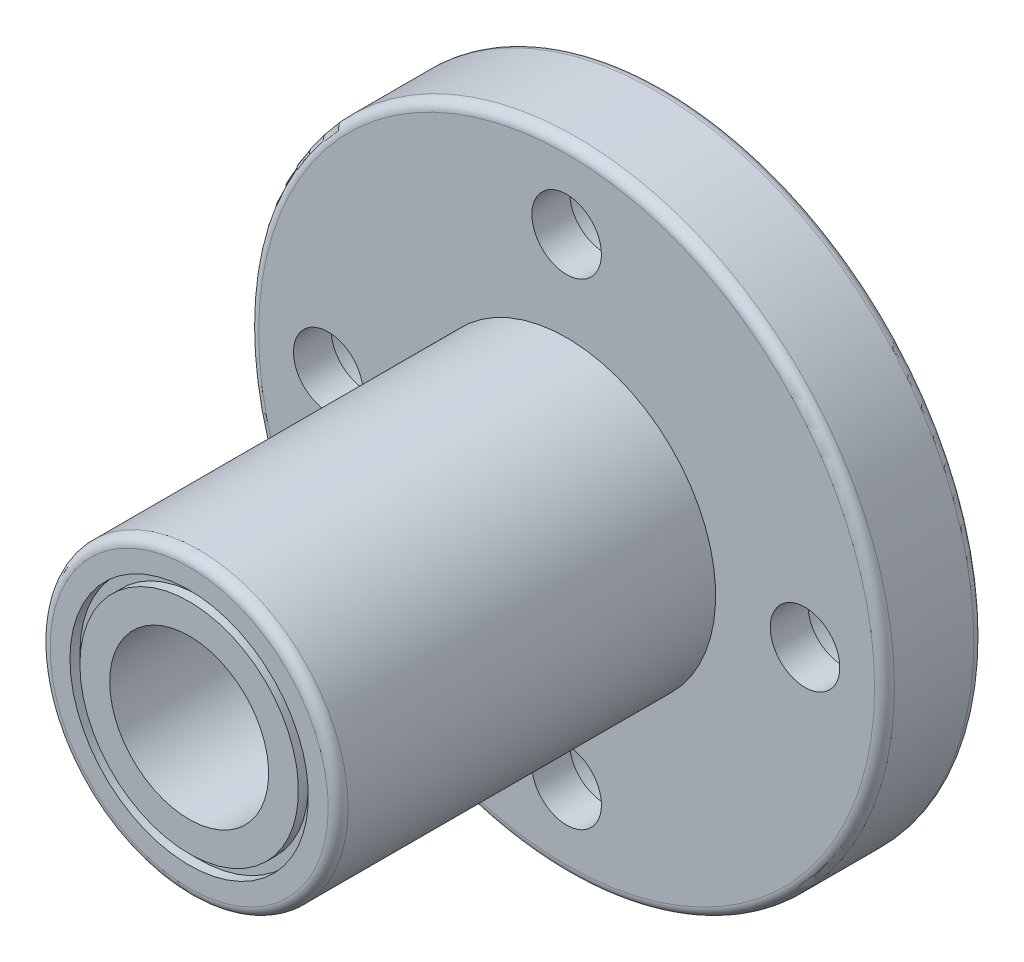
SolidWorks part; units mm, degrees
material "AISI 316 Отожженная нержавеющая сталь. полоса (SS)"
ref_plane "Plano frontal" through (0, 0, 0) normal (0, 0, 1) x (1, 0, 0)
ref_plane "Plano superior" through (0, 0, 0) normal (0, 1, 0) x (1, 0, 0)
ref_plane "Plano direito" through (0, 0, 0) normal (1, 0, 0) x (0, 0, -1)
sketch "Esboço1" plane through (0, 0, 0) normal (1, 0, 0) x (0, 0, -1)
  line L0 (0, 4) -> (0, 5.5)
  line L1 (0, 16) -> (-5, 16)
  line L2 (-5, 16) -> (-5, 7.5)
  line L3 (-5, 7.5) -> (-24, 7.5)
  line L4 (-24, 7.5) -> (-24, 6)
  line L5 (-24, 4) -> (0, 4)
  line L6 (0, 0) -> (-226.2321, 0) construction
  line L7 (-24, 6) -> (-23.5, 6)
  line L8 (-23.5, 6) -> (-23.5, 5.5)
  line L9 (-23.5, 5.5) -> (-24, 5.5)
  line L10 (0, 7.5) -> (-0.5, 7.5)
  line L11 (-0.5, 7.5) -> (-0.5, 7)
  line L12 (-0.5, 7) -> (0, 7)
  line L13 (0, 7.5) -> (0, 16)
  line L14 (-24, 5.5) -> (-24, 4)
  line L15 (0, 6) -> (-0.5, 6)
  line L16 (-0.5, 6) -> (-0.5, 5.5)
  line L17 (-0.5, 5.5) -> (0, 5.5)
  line L18 (0, 6) -> (0, 7)
  dimension "D1" = 24
  dimension "D2" = 15
  dimension "D3" = 8
  dimension "D4" = 32
  dimension "D5" = 5
  dimension "D6" = 0.5
  dimension "D7" = 0.5
  dimension "D8" = 0.5
  dimension "D9" = 0.5
  dimension "D10" = 0.5
  dimension "D11" = 0.5
revolve "Revolução1" add sketch "Esboço1" angle 360 about L6
sketch "Esboço5" plane through (0, 0, 0) normal (1, 0, 0) x (0, 0, -1)
  line L0 (0, 15) -> (-3.1, 15)
  line L1 (0, -16) -> (0, 16) construction
  line L2 (-3.1, 15) -> (-3.1, 13.75)
  line L3 (-3.1, 13.75) -> (-5, 13.75)
  line L4 (-5, 16) -> (-5, -16) construction
  line L5 (-5, 13.75) -> (-5, 12)
  line L6 (-5, 12) -> (0, 12)
  line L7 (0, 12) -> (0, 15)
  line L8 (0, 12) -> (2.2336, 12) construction
  line L9 (0, 0) -> (9.7959, 0) construction
  dimension "D1" = 6
  dimension "D2" = 3.5
  dimension "D3" = 3.1
  dimension "D4" = 24
revolve "Corte-Revolução1" cut sketch "Esboço5" angle 360 about L8
pattern_circular "PadrãoCircular1" count 4 over 360 about axis through (0, 0, 0) along (0, 0, 1) of "Corte-Revolução1"
fillet "Filete1" radius 0.5 3 edges at (-16, 0, 0) (-16, 0, 5) (-7.5, 0, 24)
